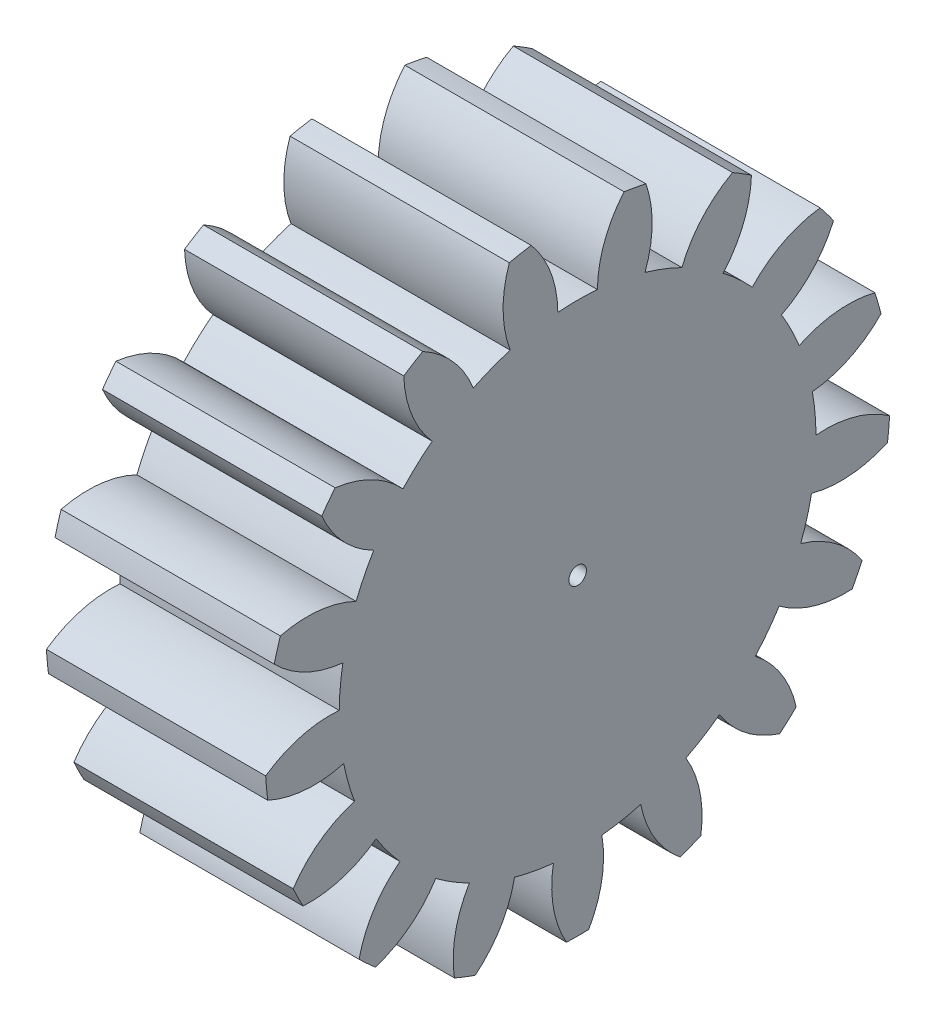
SolidWorks part; units mm, degrees
ref_plane "Plane1" through (0, 0, 0) normal (0, 0, 1) x (1, 0, 0)
ref_plane "Plane2" through (0, 0, 0) normal (0, 1, 0) x (1, 0, 0)
ref_plane "Plane3" through (0, 0, 0) normal (1, 0, 0) x (0, 0, -1)
sketch "HoldingSke" plane through (0, 0, 0) normal (0, 1, 0) x (1, 0, 0)
  line L0 (0, 0) -> (0.6375, -0.1949)
  line L1 (-15, 0) -> (100, 0) construction
  line L2 (0, 0) -> (-2.1039, 2.3779)
  line L3 (0, 0) -> (-11.863, 4.5341)
  line L4 (0, 0) -> (8.2586, 2.5249)
  line L5 (0, 0) -> (-46.8476, -17.4728)
  line L6 (0, 0) -> (-8.2896, -5.593)
  line L7 (-2.1039, 2.3779) -> (8.6586, 51.2059)
  line L8 (-76.2, 54.61) -> (-76.1, 54.61)
  line L9 (-67.7845, 28.3722) -> (-49.3413, 33.142)
  line L10 (-76.2, 71.12) -> (104.1128, 71.12)
  line L11 (0, 0) -> (-10, 0)
  line L12 (-76.2, 101.6) -> (-76.147, 101.6)
  line L13 (24.9733, 27.94) -> (52.9518, 28.4284)
  line L14 (24.9733, 27.94) -> (24.9743, 27.94)
  line L15 (24.9733, 27.94) -> (100.4006, 29.5858)
  line L16 (-63.627, -1.5) -> (-12.827, -1.5)
  circle A0 centre (0, 0) radius 0.4
  circle A1 centre (0, 0) radius 10.874
  circle A2 centre (0, 0) radius 37.5
  circle A3 centre (0, 0) radius 0.4
  dimension "MHD" = 21.748
  dimension "Hub_dia" = 75
  dimension "Bore" = 0.8
  dimension "MBD" = 0.8
  dimension "Num_teeth" = 17
  dimension "Pitch" = 0.6667
  dimension "Overall_len" = 50
  dimension "Show_teeth" = 17
  dimension "Thickness" = 10
  dimension "OAL" = 50.0001
  dimension "T_dim" = 0.1
  dimension "Ap" = 14.5
  dimension "H" = 19.05
  dimension "Pitch_radius" = 180.3128
  dimension "Width" = 10
  dimension "Backlash" = 0.053
  dimension "Addendum_fac" = 1
  dimension "Dedendum_fac" = 1.25
  dimension "Clearance_fac" = 0.25
  dimension "Dedendum_add" = 0.001
  dimension "Module" = 1.5
sketch "BasProSke" plane through (0, 0, 0) normal (0, 1, 0) x (1, 0, 0)
  line L0 (-10, 0) -> (60, 0) construction
  line L1 (0, 0) -> (0, 14.25)
  line L2 (0, 0) -> (10, 0)
  line L3 (10, 0) -> (10, 14.25)
  line L4 (10, 14.25) -> (0, 14.25)
  dimension "Thickness" = 10
  dimension "Diameter" = 28.5
revolve "Base-Revolve" add sketch "BasProSke" angle 360 about L0
sketch "TooCutSke" plane through (0, 0, 0) normal (1, 0, 0) x (0, 0, -1)
  line L1 (0, 0) -> (0, 107) construction
  line L2 (0, 0) -> (-1.2691, 12.6867) construction
  line L3 (0, 0) -> (-4.6687, 24.9751) construction
  line L4 (-1.2691, 12.6867) -> (-2.3343, 12.4876) construction
  arc A0 (0.9021, 10.8365) -> (-0.9021, 10.8365) centre (0, 0) ccw
  arc A1 (2.1374, 14.1145) -> (-2.1374, 14.1145) centre (0, 0) ccw
  circle A2 centre (0, 0) radius 12.75 construction
  circle A3 centre (0, 0) radius 12.3439 construction
  arc A4 (-0.9021, 10.8365) -> (-2.1374, 14.1145) centre (-6.0019, 10.7865) ccw
  arc A5 (2.1374, 14.1145) -> (0.9021, 10.8365) centre (6.0019, 10.7865) ccw
  dimension "Root_dia" = 21.748
  dimension "Overcut_dia" = 28.5508
  dimension "Pitch_dia" = 25.5
  dimension "Base_dia" = 24.6878
  dimension "Flank_rad" = 5.1
  dimension "Half_ang" = 10.588
  dimension "Half_CT" = 1.0837
extrude "ToothCut" cut sketch "TooCutSke" along normal through all
fillet "Breaks" [suppressed] radius 0.03
fillet "RootFillets" [suppressed] radius 0.376
pattern_circular "TeethCuts" count 17 every 21.176 about axis through (-10, 0, 0) along (1, 0, 0) of "ToothCut", "RootFillets", "Breaks"
sketch "HubNeaOneSke" plane through (0, 0, 0) normal (-1, 0, 0) x (0, 0, 1)
  circle A0 centre (0, 0) radius 10.874
  dimension "Diameter" = 21.748
extrude "HubNearOne" [suppressed] add sketch "HubNeaOneSke" along normal blind 40.0001
sketch "HubNeaBotSke" plane through (0, 0, 0) normal (-1, 0, 0) x (0, 0, 1)
  circle A0 centre (0, 0) radius 10.874
  dimension "Diameter" = 21.748
extrude "HubNearBoth" [suppressed] add sketch "HubNeaBotSke" along normal blind 20
ref_plane "FarPln" through (10, 0, 0) normal (1, 0, 0) x (0, 0, -1)
sketch "HubFarSke" plane through (10, 0, 0) normal (1, 0, 0) x (0, 0, -1)
  circle A0 centre (0, 0) radius 10.874
  dimension "Diameter" = 21.748
extrude "HubFar" [suppressed] add sketch "HubFarSke" along normal blind 20
sketch "BorSke" plane through (0, 0, 0) normal (1, 0, 0) x (0, 0, -1)
  circle A0 centre (0, 0) radius 0.4
  dimension "Diameter" = 0.8
extrude "Bore" cut sketch "BorSke" along normal mid plane 100.0001
sketch "KeySke" plane through (0, 0, 0) normal (1, 0, 0) x (0, 0, -1)
  line L0 (-0.05, 0) -> (-0.05, 0.5)
  line L1 (-0.05, 0.5) -> (0.05, 0.5)
  line L2 (0.05, 0.5) -> (0.05, 0)
  line L3 (0, 0) -> (0, 34) construction
  line L4 (-0.05, 0) -> (0.05, 0)
  dimension "Offset" = 0.5
  dimension "Width" = 0.1
extrude "Keyway" [suppressed] cut sketch "KeySke" along normal mid plane 100.0001
pattern_circular "Keyway2" [suppressed] count 2 every 90 about axis through (-10, 0, 0) along (1, 0, 0)
equation "' \"Module@HoldingSke\" = 6.35"
equation "' \"Num_teeth@HoldingSke\" = 12"
equation "' \"Ap@HoldingSke\" =  20"
equation "' \"Ap@HoldingSke\" = 20"
equation "' \"Width@HoldingSke\" = 0.5 * 25.4"
equation "' \"Hub_dia@HoldingSke\"= 1 * 25.4"
equation "' \"Hub_dia@HoldingSke\" = 1 * 25.4"
equation "' \"Overall_len@HoldingSke\" = 1.0 * 25.4"
equation "' \"Bore@HoldingSke\" = 0.75 * 25.4"
equation "' \"T_dim@HoldingSke\" = 0.1 * 25.4"
equation "' \"Width@KeySke\" = 0.25 * 25.4"
equation "' \"Show_teeth@HoldingSke\" = 13"
equation "' \"Backlash@HoldingSke\" = 0.009 * 25.4"
equation "' \"Addendum_fac@HoldingSke\" = 1.0"
equation "' \"Dedendum_fac@HoldingSke\" = 1.25"
equation "' \"Dedendum_add@HoldingSke\" = 0.00005 * 25.4"
equation "' \"Clearance_fac@HoldingSke\" = 0.25"
equation "\"Pitch@HoldingSke\" = 1 / \"Module@HoldingSke\""
equation "\"Overcut_dia@TooCutSke\" = (\"Num_teeth@HoldingSke\" + 2 * \"Addendum_fac@HoldingSke\") / \"Pitch@HoldingSke\" + 0.002 * 25.4"
equation "\"Pitch_dia@TooCutSke\" = \"Num_teeth@HoldingSke\" / \"Pitch@HoldingSke\""
equation "\"Base_dia@TooCutSke\" = \"Num_teeth@HoldingSke\" / \"Pitch@HoldingSke\" * cos((\"Ap@HoldingSke\"  * 3.14159265 / 180))"
equation "\"Root_dia@TooCutSke\" = (\"Num_teeth@HoldingSke\" + 2) / \"Pitch@HoldingSke\" - 2 * (\"Addendum_fac@HoldingSke\" + \"Dedendum_fac@HoldingSke\") / \"Pitch@HoldingSke\" - \"Dedendum_add@HoldingSke\" * 2"
equation "\"Half_ang@TooCutSke\" = 180 / \"Num_teeth@HoldingSke\""
equation "\"Half_CT@TooCutSke\" = \"Num_teeth@HoldingSke\" / \"Pitch@HoldingSke\" * sin((3.14159265 / 2 / \"Num_teeth@HoldingSke\")) / 2 - 7 * \"Backlash@HoldingSke\" / 4"
equation "\"Flank_rad@TooCutSke\" = \"Num_teeth@HoldingSke\" / \"Pitch@HoldingSke\" / 5"
equation "\"Radius@RootFillets\" = \"Clearance_fac@HoldingSke\" / \"Pitch@HoldingSke\" + \"Dedendum_add@HoldingSke\""
equation "\"Break_rad@Breaks\" = 0.02 / \"Pitch@HoldingSke\""
equation "\"Thickness@HoldingSke\" = \"Width@HoldingSke\""
equation "\"OAL@HoldingSke\" = \"Thickness@HoldingSke\""
equation "\"MHD@HoldingSke\" = (\"Num_teeth@HoldingSke\" + 2) / \"Pitch@HoldingSke\" - 2 * (\"Addendum_fac@HoldingSke\" + \"Dedendum_fac@HoldingSke\")  / \"Pitch@HoldingSke\" - \"Dedendum_add@HoldingSke\" * 2"
equation "\"MBD@HoldingSke\" = (\"Num_teeth@HoldingSke\" + 2) / \"Pitch@HoldingSke\" - 2 * (\"Addendum_fac@HoldingSke\" + \"Dedendum_fac@HoldingSke\")  / \"Pitch@HoldingSke\" - \"Dedendum_add@HoldingSke\" * 2 - 0.002 * 25.4"
equation "\"MHD@HoldingSke\" = ((sgn( \"MHD@HoldingSke\" - \"Hub_dia@HoldingSke\" )-1)*( \"MHD@HoldingSke\" - \"Hub_dia@HoldingSke\" ))/-2+ \"Hub_dia@HoldingSke\""
equation "\"MBD@HoldingSke\" = ((sgn( \"MBD@HoldingSke\" - \"Bore@HoldingSke\" )-1)*( \"MBD@HoldingSke\" - \"Bore@HoldingSke\" ))/-2+ \"Bore@HoldingSke\""
equation "\"OAL@HoldingSke\" = ((sgn( \"OAL@HoldingSke\" - \"Overall_len@HoldingSke\" )+1)*( \"OAL@HoldingSke\" - \"Overall_len@HoldingSke\" ))/2 + \"Overall_len@HoldingSke\" + 0.000002 * 25.4"
equation "\"Num_teeth@TeethCuts\" = int( \"Show_teeth@HoldingSke\" ) + 1"
equation "\"Num_teeth@TeethCuts\" = ((sgn( \"Num_teeth@TeethCuts\" - \"Num_teeth@HoldingSke\" )-1)*( \"Num_teeth@TeethCuts\" - \"Num_teeth@HoldingSke\" ))/-2+ \"Num_teeth@HoldingSke\""
equation "\"Num_teeth@TeethCuts\" = ((sgn( \"Num_teeth@TeethCuts\" - 2.0)+1)*( \"Num_teeth@TeethCuts\" - 2.0))/2 +2.0"
equation "\"Angle@TeethCuts\" = 360.0 / \"Num_teeth@HoldingSke\""
equation "\"Diameter@BasProSke\" = (\"Num_teeth@HoldingSke\" + 2 * \"Addendum_fac@HoldingSke\") / \"Pitch@HoldingSke\""
equation "\"Thickness@BasProSke\"  = \"Thickness@HoldingSke\""
equation "' \"Fillet_rad@BasProSke\" =  \"Thickness@HoldingSke\" * 0.05"
equation "' \"Fillet_rad@BasProSke\" = \"Thickness@HoldingSke\" * 0.05"
equation "\"MHD@HoldingSke\" = ((sgn( \"MHD@HoldingSke\" - \"Root_dia@TooCutSke\" )-1)*( \"MHD@HoldingSke\" - \"Root_dia@TooCutSke\" ))/-2+ \"Root_dia@TooCutSke\""
equation "\"Diameter@HubNeaOneSke\" = \"MHD@HoldingSke\""
equation "\"Length@HubNearOne\" = \"OAL@HoldingSke\" - \"Thickness@BasProSke\""
equation "\"Diameter@HubNeaBotSke\" = \"MHD@HoldingSke\""
equation "\"Length@HubNearBoth\" = ( \"OAL@HoldingSke\" - \"Thickness@BasProSke\" ) / 2.0"
equation "\"Thickness@FarPln\" = \"Thickness@BasProSke\""
equation "\"Diameter@HubFarSke\" = \"MHD@HoldingSke\""
equation "\"Length@HubFar\" = ( \"OAL@HoldingSke\" - \"Thickness@BasProSke\" ) / 2.0"
equation "\"Diameter@BorSke\" = \"MBD@HoldingSke\""
equation "\"D1@Bore\" = \"OAL@HoldingSke\" * 2.0"
equation "\"D1@Keyway\" = \"OAL@HoldingSke\" * 2.0"
equation "\"Offset@KeySke\" = \"T_dim@HoldingSke\" + \"MBD@HoldingSke\" / 2.0"
